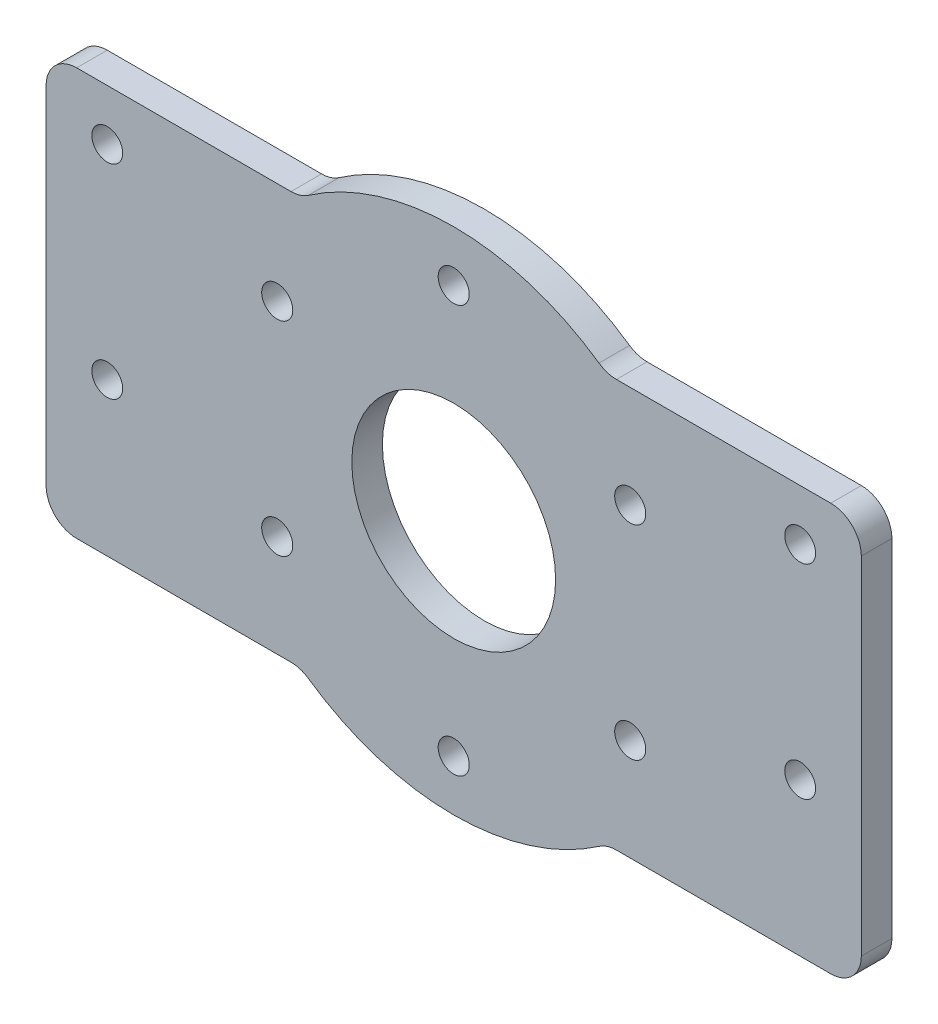
SolidWorks part; units mm, degrees
material "环氧玻璃布层压板"
ref_plane "前视基准面" through (0, 0, 0) normal (0, 0, 1) x (1, 0, 0)
ref_plane "上视基准面" through (0, 0, 0) normal (0, 1, 0) x (1, 0, 0)
ref_plane "右视基准面" through (0, 0, 0) normal (1, 0, 0) x (0, 0, -1)
sketch "草图1" plane through (0, 0, 0) normal (0, 0, 1) x (1, 0, 0)
  circle A0 centre (0, 0) radius 20 construction
  circle A1 centre (0, 0) radius 25
  circle A2 centre (0, 20) radius 1.525
  circle A3 centre (17.3205, 10) radius 1.525
  circle A4 centre (17.3205, -10) radius 1.525
  circle A5 centre (0, -20) radius 1.525
  circle A8 centre (0, 0) radius 10
  circle A9 centre (-17.3205, -10) radius 1.525
  circle A10 centre (-17.3205, 10) radius 1.525
  point P15 (0, 0)
  dimension "D1" = 40
  dimension "D2" = 50
  dimension "D3" = 3.05
  dimension "D5" = 20
  dimension "D4" = 6
extrude "凸台-拉伸1" add sketch "草图1" along normal blind 3
sketch "草图3" plane through (0, 0, 3) normal (0, 0, 1) x (1, 0, 0)
  line L0 (15, 20) -> (40, 20)
  line L1 (-40, -20) -> (-15, -20)
  line L2 (-40, -20) -> (-40, 20)
  line L3 (-40, 20) -> (-15, 20)
  line L4 (40, -20) -> (40, 20)
  line L5 (0, 20) -> (0, -20) construction
  line L6 (-40, 0) -> (40, 0) construction
  line L7 (15, -20) -> (40, -20)
  circle A0 centre (0, 0) radius 25 construction
  arc A1 (15, -20) -> (15, 20) centre (0, 0) ccw
  arc A2 (-15, 20) -> (-15, -20) centre (0, 0) ccw
  point P0 (0, 0)
  dimension "D1" = 40
  dimension "D2" = 80
extrude "凸台-拉伸2" add sketch "草图3" against normal up to surface (3 mm away) up to face at (25, 0, 0)
fillet "圆角1" radius 3 8 edges at (-15, 20, 1.5) (-40, 20, 1.5) (15, -20, 1.5) (40, -20, 1.5) (40, 20, 1.5) (15, 20, 1.5) (-15, -20, 1.5) (-40, -20, 1.5)
sketch "草图4" plane through (0, 0, 3) normal (0, 0, 1) x (1, 0, 0)
  line L0 (0, 0) -> (0, 25) construction
  circle A0 centre (-34, -5) radius 1.25 construction
  circle A1 centre (-34, 15) radius 1.25 construction
  circle A2 centre (-34, -5) radius 1.25 construction
  circle A3 centre (-34, 15) radius 1.25 construction
  circle A4 centre (-34, 15) radius 1.515
  circle A5 centre (-34, -5) radius 1.515
  arc A6 (14.2578, 20.5357) -> (-14.2578, 20.5357) centre (0, 0) ccw construction
  circle A7 centre (34, 15) radius 1.25 construction
  circle A8 centre (34, -5) radius 1.25 construction
  circle A9 centre (34, -5) radius 1.515
  circle A10 centre (34, 15) radius 1.515
  dimension "D1" = 3.03
extrude "切除-拉伸1" cut sketch "草图4" against normal blind 10
